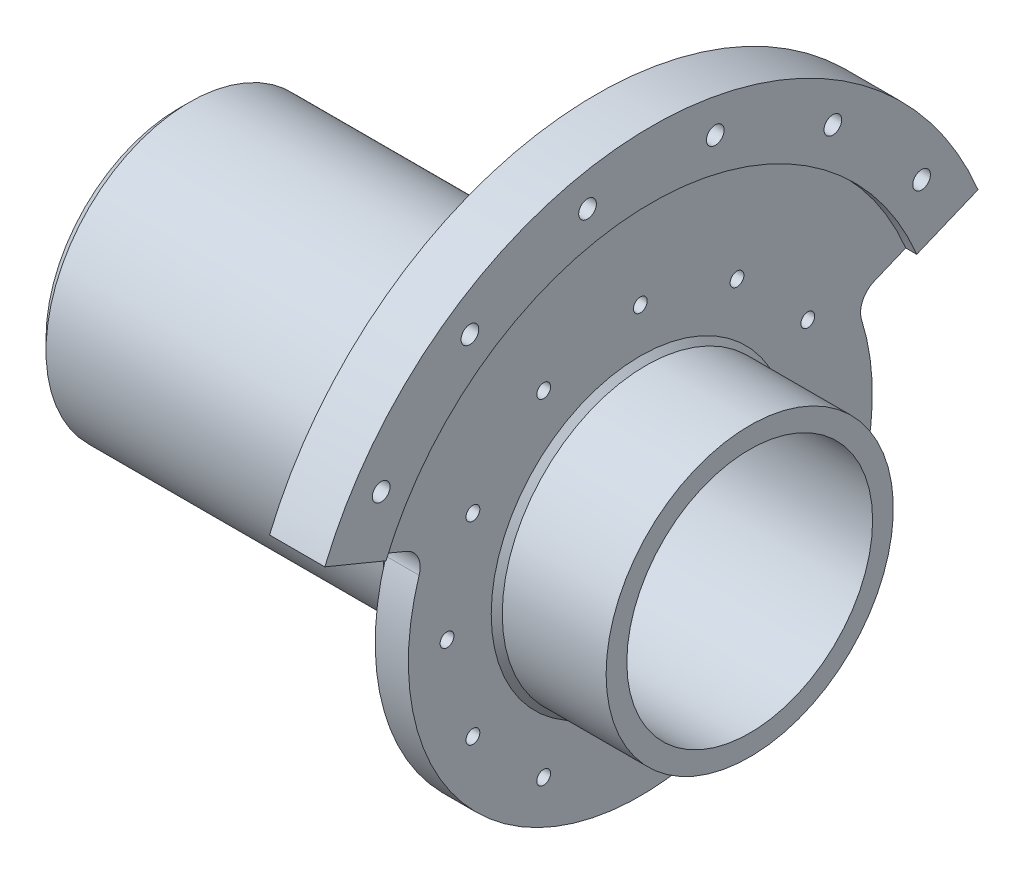
SolidWorks part; units mm, degrees
material "ABS"
ref_plane "Front Plane" through (0, 0, 0) normal (0, 0, 1) x (1, 0, 0)
ref_plane "Top Plane" through (0, 0, 0) normal (0, 1, 0) x (1, 0, 0)
ref_plane "Right Plane" through (0, 0, 0) normal (1, 0, 0) x (0, 0, -1)
sketch "Sketch1" plane through (0, 0, 0) normal (0, 0, 1) x (1, 0, 0)
  line L0 (0, 0) -> (61.0432, 0) construction
  line L1 (-40.3, 13) -> (11.4, 13)
  line L2 (-40.3, 13) -> (-40.3, 11.125)
  line L3 (-40.3, 11.125) -> (11.4, 11.125)
  line L4 (11.4, 13) -> (11.4, 11.125)
  dimension "D1" = 26
  dimension "D2" = 22.25
  dimension "D3" = 51.7
  dimension "D4" = 11.4
revolve "Revolve1" add sketch "Sketch1" angle 360 about L0
sketch "Sketch2" plane through (0, 0, 0) normal (0, 0, 1) x (1, 0, 0)
  line L0 (-40.3, 0) -> (10.8306, 0) construction
  line L1 (-40.3, 11.125) -> (-37.3, 11.125)
  line L2 (-40.3, 11.125) -> (-40.3, 7.5)
  line L3 (-40.3, 7.5) -> (-37.3, 7.5)
  line L4 (-37.3, 11.125) -> (-37.3, 7.5)
  line L5 (-40.3, 13) -> (-40.3, -13) construction
  dimension "D1" = 3
  dimension "D2" = 15
revolve "Revolve2" add sketch "Sketch2" angle 360 about L0
chamfer "Chamfer1" distance 1 angle 45 1 edges at (-40.3, 0, 13)
hole_wizard "M2 Clearance Hole1" positions "Sketch5" profile "Sketch4" hole size "M2" standard "DIN"
sketch "Sketch5" plane through (-40.3, 0, 0) normal (-1, 0, 0) x (0, 0, 1)
  circle A0 centre (0, 0) radius 9.5
  point P0 (0, 9.5)
  dimension "D1" = 19
sketch "Sketch4" plane through (-40.3, 9.5, 0) normal (0, 1, 0) x (0, 0, 1)
  line L0 (0, 0) -> (0, 11.5)
  line L1 (0, 11.5) -> (1.2, 11.5)
  line L2 (1.2, 11.5) -> (1.2, 0)
  line L5 (1.2, 0) -> (0, 0)
  line L10 (0, 11.5) -> (-1.2, 11.5) construction
  line L11 (0, -6.35) -> (0, 107.95) construction
  dimension "Hole Dia." = 2.4
  dimension "Hole Depth" = 11.5
  dimension "Drill Angle" = 180
pattern_circular "CirPattern1" count 6 over 360 about axis through (0, 0, 0) along (1, 0, 0) of "M2 Clearance Hole1"
sketch "Sketch6" plane through (0, 0, 0) normal (0, 0, 1) x (1, 0, 0)
  line L0 (11.4, 13) -> (-39.3, 13) construction
  line L1 (1.5, 13) -> (-1.5, 13)
  line L2 (1.5, 13) -> (1.5, 32)
  line L3 (1.5, 32) -> (-1.5, 32)
  line L4 (-1.5, 13) -> (-1.5, 32)
  line L5 (1.5, 13) -> (-1.5, 32) construction
  line L6 (1.5, 32) -> (-1.5, 13) construction
  line L7 (0, 0) -> (16.7478, 0) construction
  point P0 (0, 22.5)
  dimension "D1" = 3
  dimension "D2" = 64
revolve "Revolve3" add sketch "Sketch6" angle 135 mid plane about L7
sketch "Sketch9" plane through (0, 0, 0) normal (0, 0, 1) x (1, 0, 0)
  line L1 (1.5, 21) -> (-1.5, 21)
  line L2 (1.5, 21) -> (1.5, 13)
  line L3 (1.5, 13) -> (-1.5, 13)
  line L4 (-1.5, 21) -> (-1.5, 13)
  line L6 (-1.5, 13) -> (-39.3, 13) construction
  line L8 (0, 0) -> (18.5465, 0) construction
  line L9 (0, 0) -> (0, 27.1673) construction
  dimension "D1" = 42
  dimension "D2" = 3
revolve "Revolve4" add sketch "Sketch9" angle 360 about L8
sketch "Sketch10" plane through (-1.5, 0, 0) normal (-1, 0, 0) x (0, 0, 1)
  line L0 (18.4662, 10) -> (55.6473, 5.965)
  line L1 (99.6548, 0) -> (0, 0) construction
  line L2 (18.4662, -10) -> (55.6473, -5.965)
  line L3 (18.4662, 10) -> (18.4662, -10) construction
  circle A0 centre (0, 0) radius 13.5
  arc A1 (18.4662, 10) -> (18.4662, -10) centre (0, 0) ccw
  circle A3 centre (0, 0) radius 13 construction
  circle A4 centre (39.5, 0) radius 3
  circle A5 centre (55, 0) radius 3
  arc A6 (55.6473, -5.965) -> (55.6473, 5.965) centre (55, 0) ccw
  dimension "D1" = 42
  dimension "D2" = 0.5
  dimension "D3" = 15.5
  dimension "D5" = 6
  dimension "D6" = 3
  dimension "D4" = 55
  dimension "D7" = 20
chamfer "Chamfer2" distance 0.5 angle 45 2 edges at (-1.5, 0, 13) (1.5, 0, 13)
sketch "Sketch11" plane through (0, 0, 0) normal (0, 0, 1) x (1, 0, 0)
  line L0 (0, 0) -> (20.6708, 0) construction
  line L1 (1.5, 32) -> (-3.5, 32)
  line L2 (1.5, 32) -> (1.5, 26)
  line L3 (1.5, 26) -> (-3.5, 26)
  line L4 (-3.5, 32) -> (-3.5, 26)
  dimension "D1" = 5
  dimension "D2" = 52
revolve "Revolve5" add sketch "Sketch11" angle 135 mid plane about L0
sketch "Sketch12" plane through (1.5, 0, 0) normal (1, 0, 0) x (0, 0, -1)
  point P0 (24.4584, 15.5817)
  point P1 (16.4258, 23.8997)
  point P2 (5.7817, 28.4178)
  point P3 (-5.7817, 28.4178)
  point P4 (-16.4258, 23.8997)
  point P5 (-24.4584, 15.5817)
chamfer "Chamfer4" distance 1 angle 45 1 edges at (-3.5, 32, 0)
hole_wizard "Tap Drill for M1.6 Tap1" positions "Sketch16" profile "Sketch15" hole size "M1.6" standard "DIN"
sketch "Sketch16" plane through (-1.5, 0, 0) normal (-1, 0, 0) x (0, 0, 1)
  circle A0 centre (0, 0) radius 17.5
  point P0 (0, 17.5)
  dimension "D1" = 35
sketch "Sketch15" plane through (-1.5, 17.5, 0) normal (0, 1, 0) x (0, 0, 1)
  line L0 (0, 0) -> (0, 11.5)
  line L1 (0, 11.5) -> (0.625, 11.5)
  line L2 (0.625, 11.5) -> (0.625, 0)
  line L5 (0.625, 0) -> (0, 0)
  line L10 (0, 11.5) -> (-0.625, 11.5) construction
  line L11 (0, -6.35) -> (0, 107.95) construction
  dimension "Hole Dia." = 1.25
  dimension "Hole Depth" = 11.5
  dimension "Drill Angle" = 180
pattern_circular "CirPattern2" count 12 over 360 about axis through (0, 0, 0) along (1, 0, 0) of "Tap Drill for M1.6 Tap1"
fillet "Fillet1" radius 2 2 edges at (0, 8.0364, -19.4015) (0, 8.0364, 19.4015)
sketch "Sketch17" plane through (0, 0, 0) normal (0, 0, 1) x (1, 0, 0)
  line L0 (-2, 13) -> (-39.3, 13) construction
  line L1 (-4.3, 13) -> (-6.8, 13)
  line L2 (-4.3, 13) -> (-4.3, 14.95)
  line L3 (-4.3, 14.95) -> (-6.8, 14.95)
  line L4 (-6.8, 13) -> (-6.8, 14.95)
  line L5 (-40.3, 12) -> (-40.3, -12) construction
  line L6 (0, 0) -> (-56.4885, 0) construction
  dimension "D1" = 2.5
  dimension "D2" = 33.5
  dimension "D3" = 29.9
revolve "Revolve6" add sketch "Sketch17" angle 360 about L6
sketch "Esquisse1" plane through (0, 0, 0) normal (0, -0.9239, 0.3827) x (1, 0, 0)
  line L0 (-3.5, 31) -> (-2.5, 32)
  line L1 (-2.5, 32) -> (-3.5, 31) construction
  line L2 (-2.5, 32) -> (-2.5, 26)
  line L3 (-3.5, 26) -> (-1.5, 26) construction
  line L4 (-2.5, 26) -> (-3.5, 26)
  line L5 (-3.5, 26) -> (-3.5, 31)
  line L6 (-40.3, 0) -> (11.4, 0) construction
  line L7 (-40.3, 12) -> (-40.3, -12) construction
  line L8 (11.4, -13) -> (11.4, 13) construction
  dimension "D1" = 1
revolve "Enlèvement de matière-Révolution1" cut sketch "Esquisse1" angle 360 about L6
sketch "Esquisse2" plane through (0, 0, 0) normal (0, -0.9239, 0.3827) x (1, 0, 0)
  line L0 (1.5, 32) -> (2.5, 32)
  line L1 (2.5, 32) -> (2.5, 26)
  line L2 (2.5, 26) -> (1.5, 26)
  line L3 (1.5, 22.9129) -> (1.5, 32) construction
  line L4 (1.5, 26) -> (1.5, 32)
  line L5 (11.4, 0) -> (-40.3, 0) construction
  line L6 (11.4, -13) -> (11.4, 13) construction
  line L7 (-40.3, 12) -> (-40.3, -12) construction
  dimension "D1" = 1
revolve "Révolution4" add sketch "Esquisse2" angle 135 about L5
hole_wizard "Trou pour taraudage pour trou taraudé M21" positions "Sketch14" profile "Sketch13" hole size "M2" standard "DIN"
sketch "Sketch14" plane through (1.5, 0, 0) normal (1, 0, 0) x (0, 0, -1)
  point P0 (16.4258, 23.8997)
  point P1 (24.4584, 15.5817)
  point P3 (5.7817, 28.4178)
  point P5 (-5.7817, 28.4178)
  point P7 (-16.4258, 23.8997)
  point P9 (-24.4584, 15.5817)
sketch "Sketch13" plane through (1.5, 23.8997, -16.4258) normal (0, 1, 0) x (0, 0, -1)
  line L0 (0, -1) -> (0, 40.8)
  line L1 (0, 40.8) -> (0.8, 40.8)
  line L2 (0.8, 40.8) -> (0.8, -1)
  line L3 (-45.9899, -1) -> (13.1384, -1) construction
  line L5 (0.8, -1) -> (0, -1)
  line L10 (0, 40.8) -> (-0.8, 40.8) construction
  line L11 (0, -7.35) -> (0, 106.95) construction
  dimension "Diamètre du perçage" = 1.6
  dimension "Profondeur du perçage" = 41.8
  dimension "Angle de pointe" = 180
